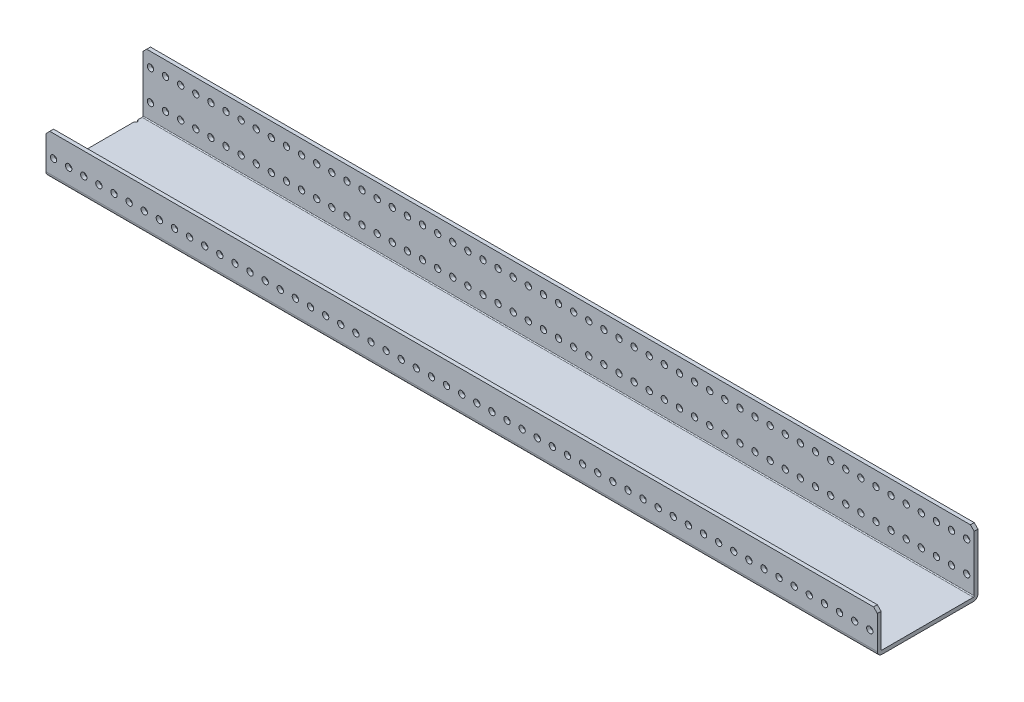
SolidWorks part; units mm, degrees
ref_plane "Front Plane" through (0, 0, 0) normal (0, 0, 1) x (1, 0, 0)
ref_plane "Top Plane" through (0, 0, 0) normal (0, 1, 0) x (1, 0, 0)
ref_plane "Right Plane" through (0, 0, 0) normal (1, 0, 0) x (0, 0, -1)
ref_plane "Plane4" through (0, 57.8164, 0) normal (0, 1, 0) x (1, 0, 0)
sketch "Sketch1" plane through (0, 57.8164, 0) normal (0, 1, 0) x (1, 0, 0)
  line L0 (602.398, -145.5605) -> (602.398, -60.9785)
  line L1 (602.398, -60.9785) -> (-96.102, -60.9785)
  line L2 (-96.102, -60.9785) -> (-96.102, -145.5605)
  line L3 (-96.102, -145.5605) -> (602.398, -145.5605)
  dimension "D1" = 698.5
extrude "Boss-Extrude1" add sketch "Sketch1" against normal blind 34.925
sketch "Sketch2" plane through (602.398, 0, 0) normal (1, 0, 0) x (0, 0, -1)
  line L0 (-60.9785, 57.8164) -> (-142.3855, 57.8164)
  line L1 (-142.3855, 57.8164) -> (-142.3855, 26.0664)
  line L2 (-142.3855, 26.0664) -> (-60.9785, 26.0664)
  line L3 (-60.9785, 26.0664) -> (-60.9785, 57.8164)
extrude "Cut-Extrude1" cut sketch "Sketch2" against normal through all
sketch "Sketch3" plane through (0, 26.0664, 0) normal (0, 1, 0) x (-1, 0, 0)
  line L0 (96.102, 60.9785) -> (-602.398, 60.9785)
  line L1 (-602.398, 60.9785) -> (-602.398, 64.1535)
  line L2 (-602.398, 64.1535) -> (96.102, 64.1535)
  line L3 (96.102, 64.1535) -> (96.102, 60.9785)
  line L5 (-602.398, 142.3855) -> (-602.398, 60.9785) construction
  line L6 (96.102, 142.3855) -> (96.102, 60.9785) construction
extrude "Boss-Extrude2" add sketch "Sketch3" along normal blind 50.8
hole_wizard "M2 Clearance Hole1" positions "Sketch5" profile "Sketch4" hole size "M2" standard "ANSI Metric" end condition through all
sketch "Sketch5" plane through (0, 26.0664, 0) normal (0, 1, 0) x (1, 0, 0)
  point P0 (-96.102, -136.5435)
  point P1 (-96.102, -69.9955)
sketch "Sketch4" plane through (-96.102, 26.0664, 136.5435) normal (1, 0, 0) x (0, 0, 1)
  line L0 (0, 0) -> (0, 3.175)
  line L1 (0, 3.175) -> (1.27, 3.175)
  line L2 (1.27, 3.175) -> (1.27, 0)
  line L5 (1.27, 0) -> (0, 0)
  line L11 (0, -6.35) -> (0, 107.95) construction
  dimension "Thru Hole Dia." = 2.54
  dimension "Thru Hole Depth" = 3.175
hole_wizard "M5 Clearance Hole1" positions "Sketch7" profile "Sketch6" hole size "M5" standard "ANSI Metric" end condition through all
sketch "Sketch7" plane through (0, 0, 60.9785) normal (0, 0, -1) x (-1, 0, 0)
  point P0 (-469.048, 64.9284)
  point P1 (-481.748, 64.9284)
  point P2 (-469.048, 39.5284)
  point P3 (-481.748, 39.5284)
  point P4 (-456.348, 39.5284)
  point P5 (-443.648, 39.5284)
  point P6 (-430.948, 39.5284)
  point P7 (-418.248, 39.5284)
  point P8 (-405.548, 39.5284)
  point P9 (-392.848, 39.5284)
  point P10 (-380.148, 39.5284)
  point P11 (-367.448, 39.5284)
  point P12 (-354.748, 39.5284)
  point P13 (-342.048, 39.5284)
  point P14 (-329.348, 39.5284)
  point P15 (-316.648, 39.5284)
  point P16 (-303.948, 39.5284)
  point P17 (-291.248, 39.5284)
  point P18 (-278.548, 39.5284)
  point P19 (-265.848, 39.5284)
  point P20 (-253.148, 39.5284)
  point P21 (-240.448, 39.5284)
  point P22 (-227.748, 39.5284)
  point P23 (-215.048, 39.5284)
  point P24 (-202.348, 39.5284)
  point P25 (-189.648, 39.5284)
  point P26 (-176.948, 39.5284)
  point P27 (-164.248, 39.5284)
  point P28 (-151.548, 39.5284)
  point P29 (-138.848, 39.5284)
  point P30 (-126.148, 39.5284)
  point P31 (-113.448, 39.5284)
  point P32 (-100.748, 39.5284)
  point P33 (-88.048, 39.5284)
  point P34 (-75.348, 39.5284)
  point P35 (-62.648, 39.5284)
  point P36 (-49.948, 39.5284)
  point P37 (-37.248, 39.5284)
  point P38 (-24.548, 39.5284)
  point P39 (-11.848, 39.5284)
  point P40 (0.852, 39.5284)
  point P41 (13.552, 39.5284)
  point P42 (26.252, 39.5284)
  point P43 (38.952, 39.5284)
  point P44 (51.652, 39.5284)
  point P45 (64.352, 39.5284)
  point P46 (77.052, 39.5284)
  point P47 (89.752, 39.5284)
  point P48 (-456.348, 64.9284)
  point P49 (-443.648, 64.9284)
  point P50 (-430.948, 64.9284)
  point P51 (-418.248, 64.9284)
  point P52 (-405.548, 64.9284)
  point P53 (-392.848, 64.9284)
  point P54 (-380.148, 64.9284)
  point P55 (-367.448, 64.9284)
  point P56 (-354.748, 64.9284)
  point P57 (-342.048, 64.9284)
  point P58 (-329.348, 64.9284)
  point P59 (-316.648, 64.9284)
  point P60 (-303.948, 64.9284)
  point P61 (-291.248, 64.9284)
  point P62 (-278.548, 64.9284)
  point P63 (-265.848, 64.9284)
  point P64 (-253.148, 64.9284)
  point P65 (-240.448, 64.9284)
  point P66 (-227.748, 64.9284)
  point P67 (-215.048, 64.9284)
  point P68 (-202.348, 64.9284)
  point P69 (-189.648, 64.9284)
  point P70 (-176.948, 64.9284)
  point P71 (-164.248, 64.9284)
  point P72 (-151.548, 64.9284)
  point P73 (-138.848, 64.9284)
  point P74 (-126.148, 64.9284)
  point P75 (-113.448, 64.9284)
  point P76 (-100.748, 64.9284)
  point P77 (-88.048, 64.9284)
  point P78 (-75.348, 64.9284)
  point P79 (-62.648, 64.9284)
  point P80 (-49.948, 64.9284)
  point P81 (-37.248, 64.9284)
  point P82 (-24.548, 64.9284)
  point P83 (-11.848, 64.9284)
  point P84 (0.852, 64.9284)
  point P85 (13.552, 64.9284)
  point P86 (26.252, 64.9284)
  point P87 (38.952, 64.9284)
  point P88 (51.652, 64.9284)
  point P89 (64.352, 64.9284)
  point P90 (77.052, 64.9284)
  point P91 (89.752, 64.9284)
  point P97 (-494.448, 64.9284)
  point P98 (-494.448, 39.5284)
  point P99 (-507.148, 64.9284)
  point P100 (-507.148, 39.5284)
  point P101 (-519.848, 64.9284)
  point P102 (-519.848, 39.5284)
  point P103 (-532.548, 64.9284)
  point P104 (-532.548, 39.5284)
  point P105 (-545.248, 64.9284)
  point P106 (-545.248, 39.5284)
  point P107 (-557.948, 64.9284)
  point P108 (-557.948, 39.5284)
  point P109 (-570.648, 64.9284)
  point P110 (-570.648, 39.5284)
  point P111 (-583.348, 64.9284)
  point P112 (-583.348, 39.5284)
  point P113 (-596.048, 64.9284)
  point P114 (-596.048, 39.5284)
  dimension "D1" = 10
sketch "Sketch6" plane through (469.048, 64.9284, 60.9785) normal (1, 0, 0) x (0, 1, 0)
  line L0 (0, 0) -> (0, 84.582)
  line L1 (0, 84.582) -> (2.667, 84.582)
  line L2 (2.667, 84.582) -> (2.667, 0)
  line L5 (2.667, 0) -> (0, 0)
  line L11 (0, -6.35) -> (0, 107.95) construction
  dimension "Thru Hole Dia." = 5.334
  dimension "Thru Hole Depth" = 84.582
chamfer "Chamfer1" distance 3.175 angle 45 4 edges at (602.398, 76.8664, 62.566) (-96.102, 57.8164, 143.973) (602.398, 57.8164, 143.973) (-96.102, 76.8664, 62.566)
fillet "Fillet1" radius 0.762 2 edges at (253.148, 26.0664, 64.1535) (253.148, 26.0664, 142.3855)
fillet "Fillet2" radius 3.937 2 edges at (253.148, 22.8914, 145.5605) (253.148, 22.8914, 60.9785)
